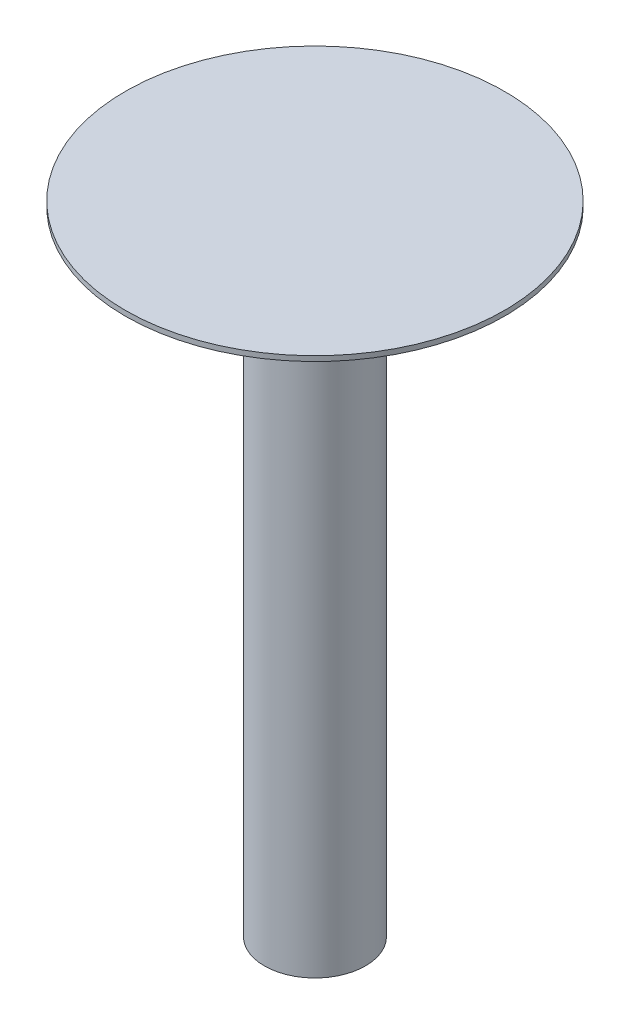
SolidWorks part; units mm, degrees
ref_plane "Face" through (0, 0, 0) normal (0, 0, 1) x (1, 0, 0)
ref_plane "Dessus" through (0, 0, 0) normal (0, 1, 0) x (1, 0, 0)
ref_plane "Droite" through (0, 0, 0) normal (1, 0, 0) x (0, 0, -1)
sketch "Esquisse1" plane through (0, 0, 0) normal (0, 1, 0) x (1, 0, 0)
  circle A0 centre (0, 0) radius 20
  dimension "D1" = 40
extrude "Extrusion1" add sketch "Esquisse1" along normal blind 250
sketch "Esquisse2" plane through (0, 250, 0) normal (0, 1, 0) x (-1, 0, 0)
  circle A0 centre (0, 0) radius 75
  dimension "D1" = 150
extrude "Extrusion2" add sketch "Esquisse2" along normal blind 2
